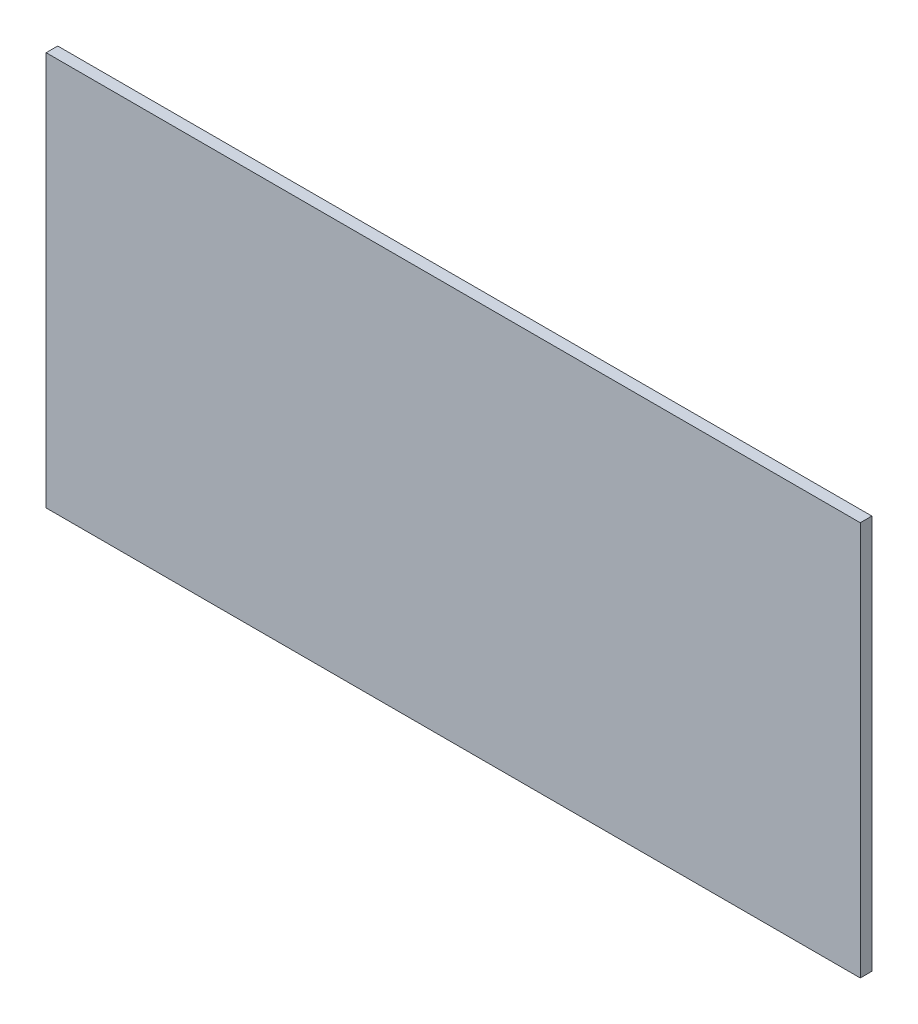
SolidWorks part; units mm, degrees
ref_plane "Front Plane" through (0, 0, 0) normal (0, 0, 1) x (1, 0, 0)
ref_plane "Top Plane" through (0, 0, 0) normal (0, 1, 0) x (1, 0, 0)
ref_plane "Right Plane" through (0, 0, 0) normal (1, 0, 0) x (0, 0, -1)
sketch "Sketch1" plane through (0, 0, 0) normal (0, 0, 1) x (1, 0, 0)
  line L1 (0, 0) -> (111.5, 0)
  line L2 (0, 0) -> (0, 54)
  line L3 (0, 54) -> (111.5, 54)
  line L4 (111.5, 0) -> (111.5, 54)
extrude "Boss-Extrude1" add sketch "Sketch1" along normal blind 1.5875
